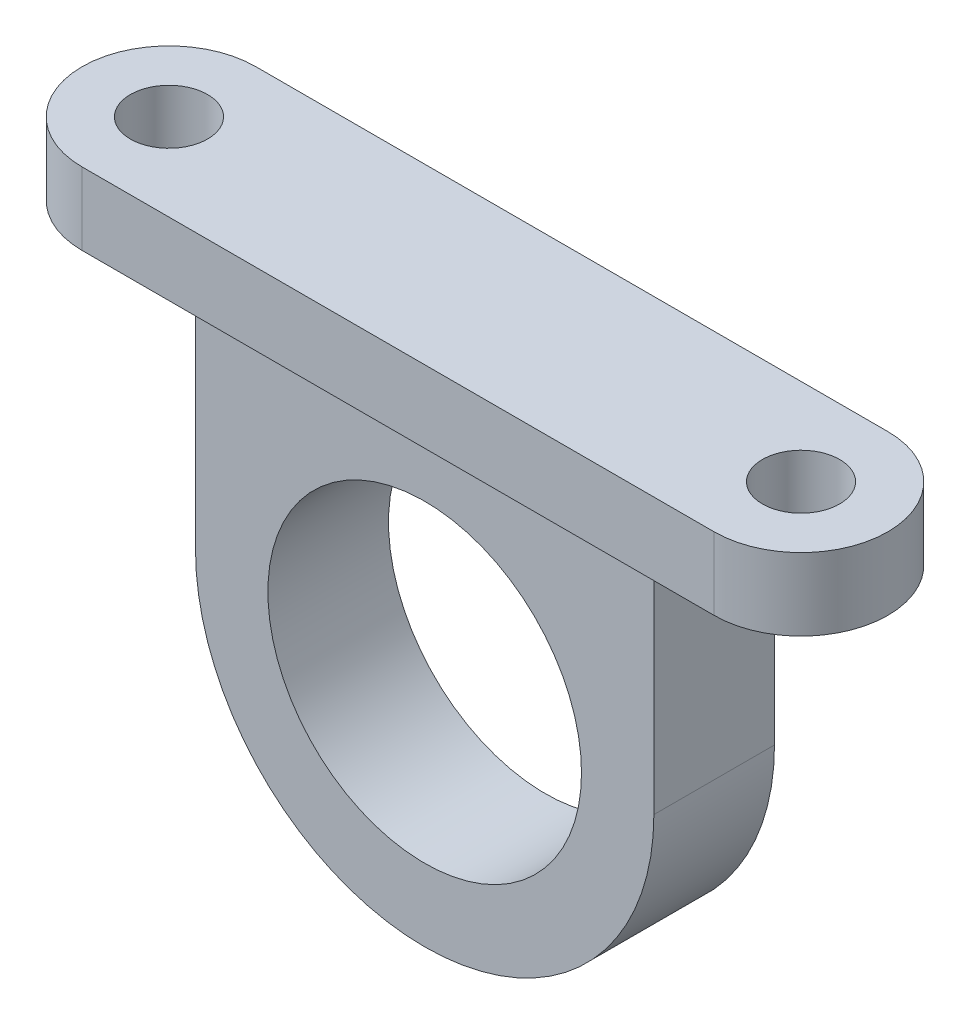
SolidWorks part; units mm, degrees
material "PLA (Orange)"
ref_plane "Front Plane" through (0, 0, 0) normal (0, 0, 1) x (1, 0, 0)
ref_plane "Top Plane" through (0, 0, 0) normal (0, 1, 0) x (1, 0, 0)
ref_plane "Right Plane" through (0, 0, 0) normal (1, 0, 0) x (0, 0, -1)
sketch "Sketch1" plane through (0, 0, 0) normal (0, 0, 1) x (1, 0, 0)
  line L0 (-9.5, 0) -> (-9.5, 9.5)
  line L1 (9.5, 0) -> (9.5, 9.5)
  line L2 (-9.5, 9.5) -> (9.5, 9.5)
  circle A0 centre (0, 0) radius 6.5
  arc A1 (-9.5, 0) -> (9.5, 0) centre (0, 0) ccw
  circle A2 centre (0, 0) radius 9.5 construction
  dimension "D1" = 13
  dimension "D3" = 9.5
  dimension "D2" = 3
extrude "Boss-Extrude1" add sketch "Sketch1" along normal blind 5
sketch "Sketch2" plane through (0, 9.5, 0) normal (0, 1, 0) x (1, 0, 0)
  line L4 (0, 1.1) -> (0, 0) construction
  line L5 (0, 0) -> (0, -5) construction
  line L15 (13.1, 1.1) -> (-13.1, 1.1)
  line L16 (9.5, -5) -> (-9.5, -5) construction
  line L22 (0, -5) -> (0, -6.1) construction
  line L23 (-9.5, -5) -> (-9.5, 0) construction
  line L31 (-13.1, -6.1) -> (13.1, -6.1)
  circle A0 centre (-13.1, -2.5) radius 1.6
  arc A1 (-13.1, 1.1) -> (-13.1, -6.1) centre (-13.1, -2.5) ccw
  arc A2 (13.1, 1.1) -> (13.1, -6.1) centre (13.1, -2.5) cw
  circle A3 centre (13.1, -2.5) radius 1.6
  dimension "D2" = 3.2
  dimension "D1" = 3.6
  dimension "D3" = 3.6
extrude "Boss-Extrude2" add sketch "Sketch2" along normal blind 3
